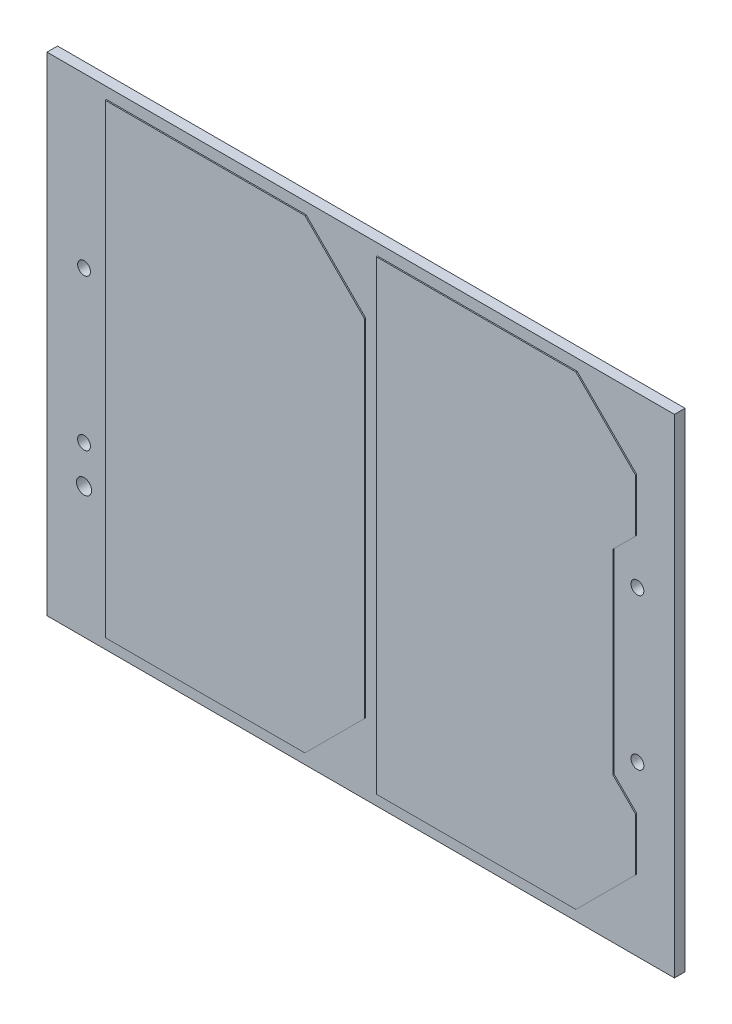
SolidWorks part; units mm, degrees
ref_plane "Front Plane" through (0, 0, 0) normal (0, 0, 1) x (1, 0, 0)
ref_plane "Top Plane" through (0, 0, 0) normal (0, 1, 0) x (1, 0, 0)
ref_plane "Right Plane" through (0, 0, 0) normal (1, 0, 0) x (0, 0, -1)
sketch "Sketch1" plane through (0, 0, 0) normal (0, 0, 1) x (1, 0, 0)
  line L0 (-46.482, 41) -> (-46.482, -41) construction
  line L1 (-52.705, -41) -> (52.705, -41)
  line L2 (-52.705, -41) -> (-52.705, 41)
  line L3 (-52.705, 41) -> (52.705, 41)
  line L4 (52.705, -41) -> (52.705, 41)
  line L5 (-52.705, -41) -> (52.705, 41) construction
  line L6 (-52.705, 41) -> (52.705, -41) construction
  line L7 (46.482, 41) -> (46.482, -41) construction
  circle A3 centre (46.482, 12.7) radius 1.0795
  circle A4 centre (46.482, -12.7) radius 1.0795
  circle A5 centre (-46.482, 12.7) radius 1.0795
  circle A6 centre (-46.482, -12.7) radius 1.0795
  circle A10 centre (-46.482, -19.05) radius 1.27
  point P0 (0, 0)
  dimension "D15" = 2.54
  dimension "D3" = 2.159
  dimension "D1" = 82
  dimension "D2" = 105.41
  dimension "D7" = 6.223
  dimension "D11" = 6.223
  dimension "D4" = 28.3
  dimension "D5" = 6.35
  dimension "D9" = 28.3
extrude "Boss-Extrude1" add sketch "Sketch1" along normal blind 1.778
sketch "Sketch2" plane through (0, 0, 1.778) normal (0, 0, 1) x (1, 0, 0)
  line L0 (-9.175, 39.095) -> (0.825, 29.095)
  line L1 (-42.705, 39.095) -> (-9.175, 39.095)
  line L2 (-42.705, 39.095) -> (-42.705, -39.095)
  line L3 (-42.705, -39.095) -> (-9.175, -39.095)
  line L4 (0.825, 29.095) -> (0.825, -29.095)
  line L5 (-42.705, 39.095) -> (0.825, -39.095) construction
  line L6 (-42.705, -39.095) -> (0.825, 39.095) construction
  line L11 (46.355, 20.205) -> (42.545, 16.395)
  line L12 (42.545, 16.395) -> (42.545, -16.395)
  line L17 (42.545, -16.395) -> (46.355, -20.205)
  line L18 (-52.705, 41) -> (52.705, 41) construction
  line L23 (-52.705, -41) -> (52.705, -41) construction
  line L24 (46.355, -20.205) -> (46.355, -29.095)
  line L43 (2.825, 39.095) -> (36.355, 39.095)
  line L44 (2.825, 39.095) -> (2.825, -39.095)
  line L45 (2.825, -39.095) -> (36.355, -39.095)
  line L46 (46.355, 29.095) -> (46.355, 20.205)
  line L47 (2.825, 39.095) -> (46.355, -39.095) construction
  line L48 (2.825, -39.095) -> (46.355, 39.095) construction
  line L49 (0.825, -29.095) -> (-9.175, -39.095)
  line L62 (36.355, -39.095) -> (46.355, -29.095)
  line L63 (36.355, 39.095) -> (46.355, 29.095)
  line L64 (-52.705, -41) -> (-52.705, 41) construction
  line L65 (52.705, -41) -> (52.705, 41) construction
  point P4 (-20.94, 0)
  point P39 (24.59, 0)
  point P76 (52.705, 0)
  dimension "D25" = 10
  dimension "D26" = 6.35
  dimension "D3" = 2
  dimension "D6" = 3.81
  dimension "D7" = 45
  dimension "D8" = 45
  dimension "D9" = 8.89
  dimension "D10" = 8.89
  dimension "D11" = 1.905
  dimension "D12" = 1.905
extrude "Boss-Extrude2" add sketch "Sketch2" along normal blind 0.2
sketch "Sketch3" plane through (0, 0, 1.978) normal (0, 0, 1) x (1, 0, 0)
  line L0 (-36.355, -32.745) -> (-36.355, 32.745)
  line L1 (-36.355, 32.745) -> (-11.8053, 32.745)
  line L2 (-11.8053, 32.745) -> (-5.525, 26.4647)
  line L3 (-5.525, 26.4647) -> (-5.525, -26.4647)
  line L4 (-5.525, -26.4647) -> (-11.8053, -32.745)
  line L5 (-11.8053, -32.745) -> (-36.355, -32.745)
  line L6 (9.175, -32.745) -> (9.175, 32.745)
  line L7 (9.175, 32.745) -> (33.7247, 32.745)
  line L8 (33.7247, 32.745) -> (40.005, 26.4647)
  line L9 (40.005, 26.4647) -> (40.005, -26.4647)
  line L10 (40.005, -26.4647) -> (33.7247, -32.745)
  line L11 (33.7247, -32.745) -> (9.175, -32.745)
  line L12 (-9.175, -39.095) -> (0.825, -29.095) construction
  line L13 (0.825, 29.095) -> (-9.175, 39.095) construction
  line L14 (-42.705, 39.095) -> (-42.705, -39.095) construction
  line L15 (0.825, -29.095) -> (0.825, 29.095) construction
  line L16 (-9.175, 39.095) -> (-42.705, 39.095) construction
  line L17 (0.825, 29.095) -> (-9.175, 39.095) construction
  line L18 (-42.705, -39.095) -> (-9.175, -39.095) construction
  line L19 (2.825, 39.095) -> (2.825, -39.095) construction
  dimension "D5" = 6.35
  dimension "D1" = 6.35
  dimension "D2" = 6.35
  dimension "D3" = 6.35
  dimension "D4" = 6.35
  dimension "D6" = 6.35
extrude "Cut-Extrude1" [suppressed] cut sketch "Sketch3" against normal through all
chamfer "Chamfer1" [suppressed] distance 2.54 angle 45
equation "\"D8@Sketch1\"=\"D6@Sketch1\""
equation "\"D4@Sketch1\"=(\"D1@Sketch1\"-\"D6@Sketch1\")/2"
equation "\"D9@Sketch1\"=\"D4@Sketch1\""
equation "\"D2@Sketch3\"=\"D1@Sketch3\""
equation "\"D3@Sketch3\"=\"D1@Sketch3\""
equation "\"D4@Sketch3\"=\"D3@Sketch3\""
equation "\"D5@Sketch3\"=\"D1@Sketch3\""
equation "\"D6@Sketch3\"=\"D1@Sketch3\""
equation "\"D7@Sketch1\"=.754/2-.141+.018/2"
equation "\"D10@Sketch2\"=\"D9@Sketch2\""
equation "\"D11@Sketch1\"=\"D7@Sketch1\""
